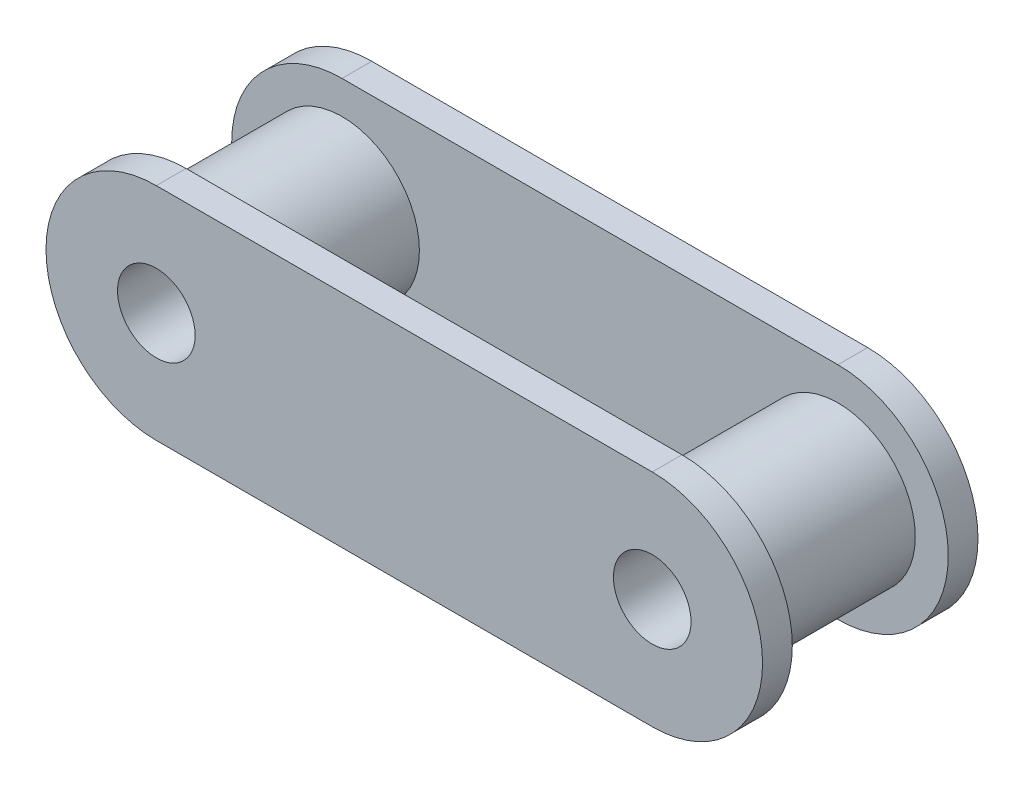
SolidWorks part; units mm, degrees
ref_plane "Front Plane" through (0, 0, 0) normal (0, 0, 1) x (1, 0, 0)
ref_plane "Top Plane" through (0, 0, 0) normal (0, 1, 0) x (1, 0, 0)
ref_plane "Right Plane" through (0, 0, 0) normal (1, 0, 0) x (0, 0, -1)
sketch "Sketch1" plane through (0, 0, 0) normal (0, 0, 1) x (1, 0, 0)
  line L0 (-12.7, 0) -> (12.7, 0) construction
  line L1 (-12.7, 5.6515) -> (12.7, 5.6515)
  line L2 (-12.7, -5.6515) -> (12.7, -5.6515)
  arc A0 (-12.7, 5.6515) -> (-12.7, -5.6515) centre (-12.7, 0) ccw
  arc A1 (12.7, -5.6515) -> (12.7, 5.6515) centre (12.7, 0) ccw
  circle A2 centre (-12.7, 0) radius 1.9875
  circle A3 centre (12.7, 0) radius 1.9875
  point P2 (0, 0)
  dimension "D2" = 25.4
  dimension "D3" = 3.9751
  dimension "D1" = 11.303
extrude "Boss-Extrude1" add sketch "Sketch1" along normal blind 1.524
ref_plane "Plane1" through (0, 0, -3.9941) normal (0, 0, 1) x (1, 0, 0)
sketch "Sketch3" plane through (0, 0, 0) normal (0, 0, -1) x (-1, 0, 0)
  circle A0 centre (-12.7, 0) radius 3.9624
  circle A1 centre (12.7, 0) radius 3.9624
  circle A2 centre (-12.7, 0) radius 1.9875 construction
  circle A3 centre (12.7, 0) radius 1.9875 construction
  circle A4 centre (-12.7, 0) radius 1.9875
  circle A5 centre (12.7, 0) radius 1.9875
  dimension "D1" = 7.9248
extrude "Boss-Extrude2" add sketch "Sketch3" along normal up to surface (3.9941 mm away) up to plane "Plane1"
mirror "Mirror4" about plane through (0, 0, -3.9941) normal (0, 0, 1) of "Boss-Extrude2", "Boss-Extrude1"
